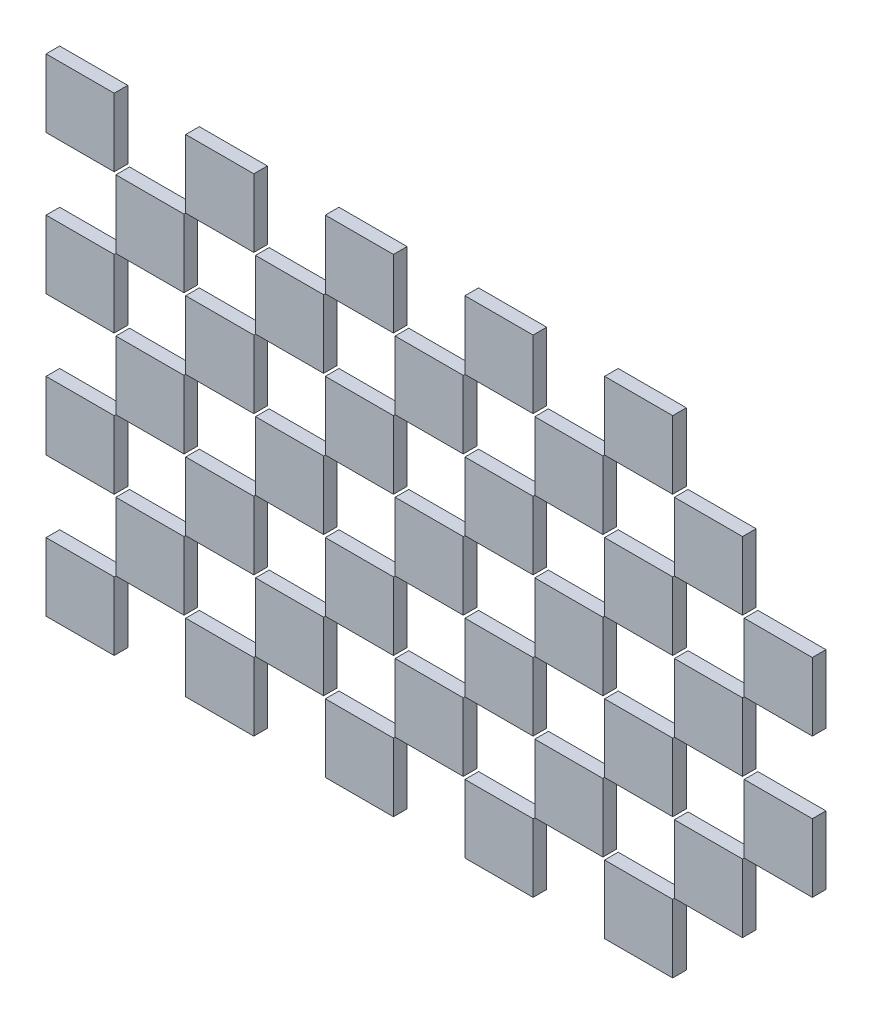
SolidWorks part; units mm, degrees
ref_plane "前视基准面" through (0, 0, 0) normal (0, 0, 1) x (1, 0, 0)
ref_plane "上视基准面" through (0, 0, 0) normal (0, 1, 0) x (1, 0, 0)
ref_plane "右视基准面" through (0, 0, 0) normal (1, 0, 0) x (0, 0, -1)
other "Configuration Table"
sketch "草图1" plane through (0, 0, 0) normal (0, 0, 1) x (1, 0, 0)
  line L1 (-6.7053, 8.1158) -> (-4.7053, 8.1158)
  line L2 (-6.7053, 8.1158) -> (-6.7053, 6.1158)
  line L3 (-6.7053, 6.1158) -> (-4.7053, 6.1158)
  line L4 (-4.7053, 8.1158) -> (-4.7053, 6.1158)
  dimension "D1" = 2
  dimension "D2" = 2
extrude "凸台-拉伸1" add sketch "草图1" along normal blind 0.4
pattern_linear "阵列(线性)1" count 4 spacing 4.1 along (0, 1, 0) count 6 spacing 4.1 along (1, 0, 0) of "凸台-拉伸1"
sketch "草图2" plane through (0, 0, 0) normal (0, 0, 1) x (1, 0, 0)
  line L5 (-4.7053, 10.2158) -> (-2.6053, 8.1158) construction
  line L6 (-2.6053, 10.2158) -> (-4.7053, 8.1158) construction
  line L7 (-4.6553, 8.1658) -> (-2.6553, 8.1658)
  line L8 (-4.6553, 8.1658) -> (-4.6553, 10.1658)
  line L9 (-4.6553, 10.1658) -> (-2.6553, 10.1658)
  line L10 (-2.6553, 8.1658) -> (-2.6553, 10.1658)
  line L11 (-4.6553, 8.1658) -> (-2.6553, 10.1658) construction
  line L12 (-4.6553, 10.1658) -> (-2.6553, 8.1658) construction
  point P0 (-3.6553, 9.1658)
  dimension "D1" = 2
extrude "凸台-拉伸2" add sketch "草图2" along normal blind 0.4 separate body
pattern_linear "阵列(线性)2" count 3 spacing 4.1 along (0, 1, 0) count 5 spacing 4.1 along (1, 0, 0) of "凸台-拉伸2"
delete or keep bodies "实体-删除/保留 1" bodies 126 129
